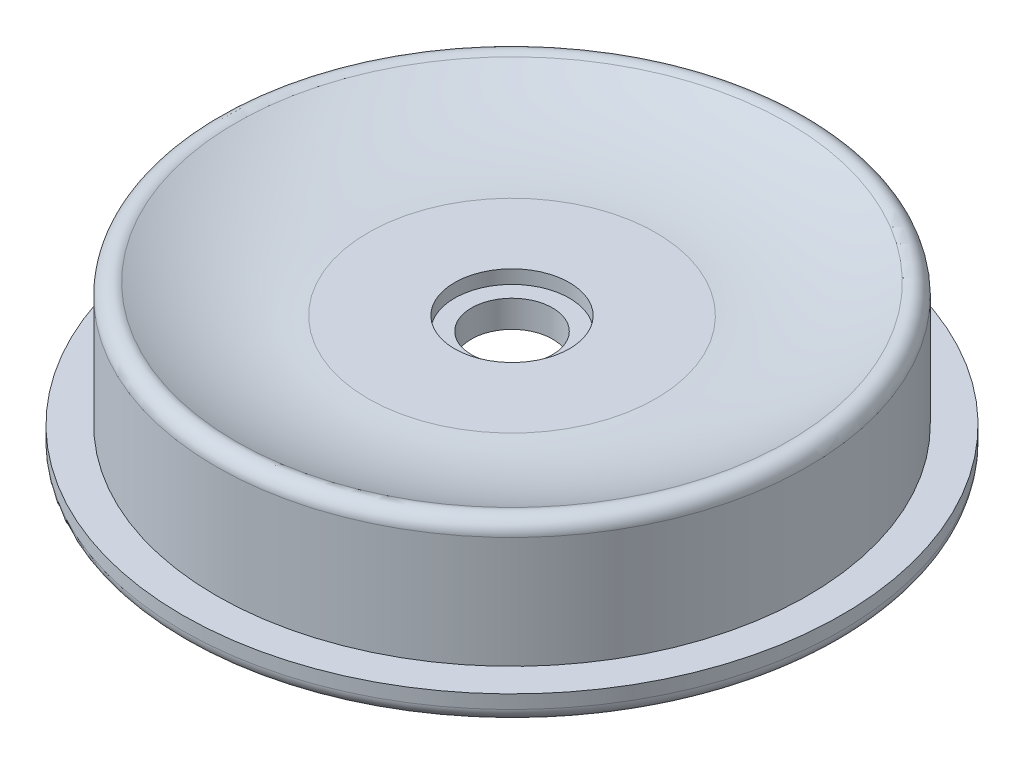
SolidWorks part; units mm, degrees
ref_plane "Front Plane" through (0, 0, 0) normal (0, 0, 1) x (1, 0, 0)
ref_plane "Top Plane" through (0, 0, 0) normal (0, 1, 0) x (1, 0, 0)
ref_plane "Right Plane" through (0, 0, 0) normal (1, 0, 0) x (0, 0, -1)
ref_axis "Axis1" through (0, 55, 0) along (0, -1, 0)
sketch "Sketch1" plane through (0, 0, 0) normal (0, 0, 1) x (1, 0, 0)
  line L0 (29, 0) -> (46.8, 0)
  line L1 (48.8, 2) -> (48.8, 4)
  line L2 (48.8, 4) -> (43.8, 4)
  line L3 (43.8, 4) -> (43.8, 20.5229)
  line L4 (8.5, 18) -> (21.3, 18)
  line L5 (0, 55) -> (0, -55) construction
  line L6 (8.5, 18) -> (8.5, 16)
  line L7 (8.5, 16) -> (6, 16)
  line L8 (6, 16) -> (6, 12)
  line L9 (6, 12) -> (29, 12)
  line L10 (29, 12) -> (29, 0)
  arc A0 (21.3, 18) -> (40.8715, 22.2943) centre (23.2297, 55.951) ccw
  arc A1 (43.8, 20.5229) -> (40.8715, 22.2943) centre (41.8, 20.5229) ccw
  arc A2 (46.8, 0) -> (48.8, 2) centre (46.8, 2) ccw
  point P13 (43.8, 24)
  point P16 (48.8, 0)
  dimension "D7" = 2
  dimension "D8" = 2
  dimension "D9" = 38
  dimension "D2" = 4
  dimension "D3" = 20
  dimension "D4" = 21.3
  dimension "D5" = 18
  dimension "D6" = 5
  dimension "D10" = 12
  dimension "D11" = 4
  dimension "D12" = 2
  dimension "D13" = 17.8
  dimension "D14" = 6
  dimension "D15" = 2.5
  dimension "D16" = 29
revolve "Revolve1" add sketch "Sketch1" angle 360 about axis through (0, 55, 0) along (0, -1, 0)
fillet "Fillet1" radius 10 1 edges at (0, 0, 29)
